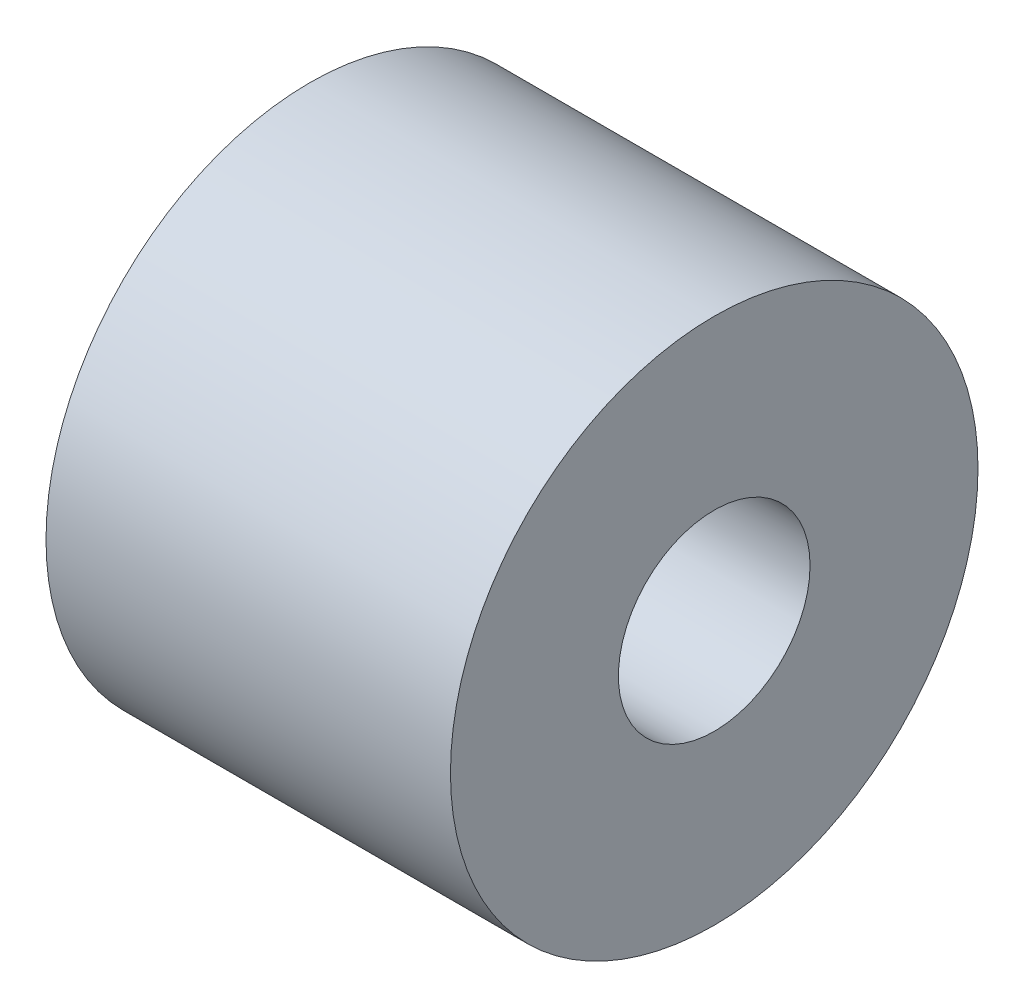
SolidWorks part; units mm, degrees
material "ABS"
ref_plane "Front Plane" through (0, 0, 0) normal (0, 0, 1) x (1, 0, 0)
ref_plane "Top Plane" through (0, 0, 0) normal (0, 1, 0) x (1, 0, 0)
ref_plane "Right Plane" through (0, 0, 0) normal (1, 0, 0) x (0, 0, -1)
sketch "Sketch1" plane through (0, 0, 0) normal (1, 0, 0) x (0, 0, -1)
  circle A0 centre (0, 0) radius 30
  circle A1 centre (0, 0) radius 9
  dimension "D1" = 18
  dimension "D2" = 60
extrude "Boss-Extrude1" add sketch "Sketch1" along normal blind 46
sketch "Sketch2" plane through (46, 0, 0) normal (1, 0, 0) x (0, 0, -1)
  circle A0 centre (0, 0) radius 10.9
  dimension "D1" = 21.8
extrude "Cut-Extrude1" cut sketch "Sketch2" against normal blind 23
